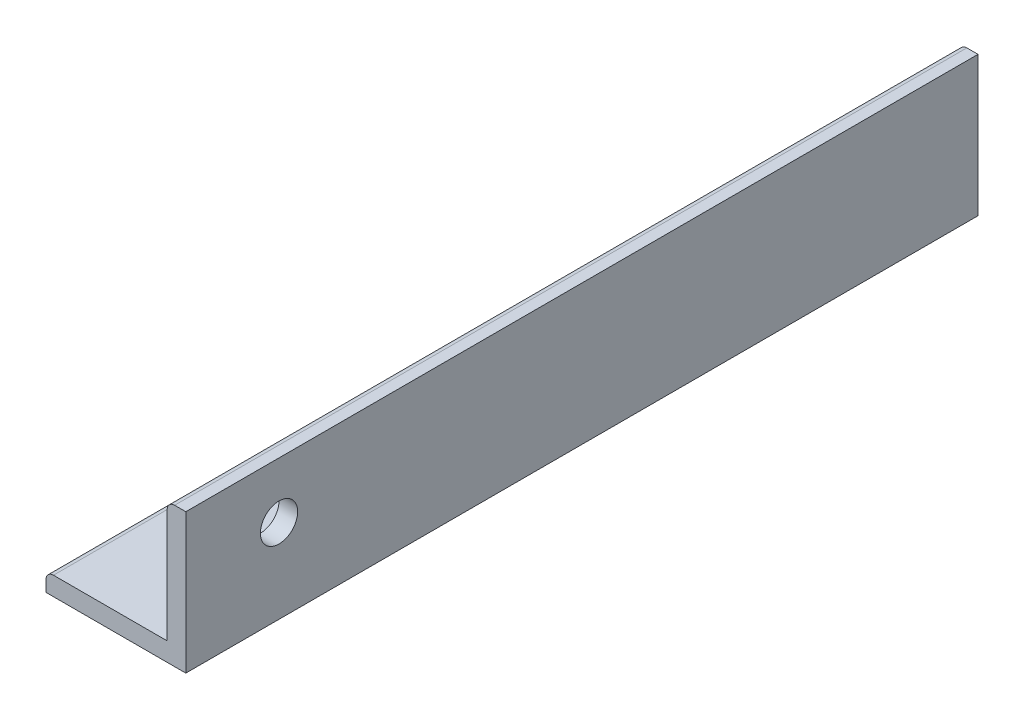
SolidWorks part; units mm, degrees
ref_plane "前视基准面" through (0, 0, 0) normal (0, 0, 1) x (1, 0, 0)
ref_plane "上视基准面" through (0, 0, 0) normal (0, 1, 0) x (1, 0, 0)
ref_plane "右视基准面" through (0, 0, 0) normal (1, 0, 0) x (0, 0, -1)
sketch "草图1" plane through (0, 0, 0) normal (0, 0, 1) x (1, 0, 0)
  line L0 (0, 0) -> (0, 15)
  line L1 (0, 15) -> (-2, 15)
  line L2 (-2, 15) -> (-2, 2)
  line L3 (0, 0) -> (-15, 0)
  line L4 (-15, 0) -> (-15, 2)
  line L5 (-15, 2) -> (-2, 2)
  dimension "D1" = 15
  dimension "D2" = 15
  dimension "D3" = 2
  dimension "D4" = 2
extrude "凸台-拉伸1" add sketch "草图1" along normal blind 85
fillet "圆角1" radius 0.8 2 edges at (-15, 2, 42.5) (-2, 15, 42.5)
sketch "草图2" plane through (0, 2, 0) normal (0, 1, 0) x (1, 0, 0)
  line L2 (-2, -85) -> (-2, 0) construction
  line L4 (-2, 0) -> (-14.2, 0) construction
  circle A1 centre (-8, -15) radius 2
  dimension "D1" = 4
  dimension "D2" = 15
  dimension "D6" = 6
extrude "切除-拉伸1" cut sketch "草图2" against normal blind 2
sketch "草图3" plane through (-2, 0, 0) normal (-1, 0, 0) x (0, 0, 1)
  line L0 (85, 14.2) -> (85, 2) construction
  line L2 (85, 2) -> (0, 2) construction
  circle A0 centre (75, 9) radius 2
  dimension "D1" = 4
  dimension "D2" = 10
  dimension "D3" = 7
extrude "切除-拉伸2" cut sketch "草图3" against normal blind 400
